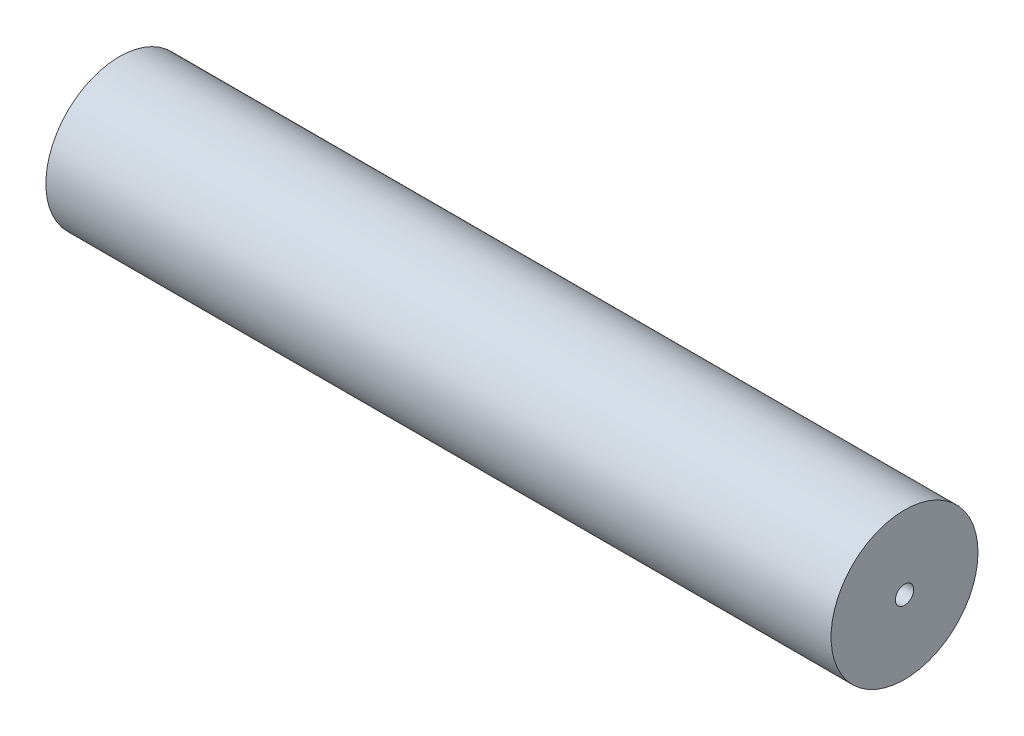
SolidWorks part; units mm, degrees
ref_plane "Front Plane" through (0, 0, 0) normal (0, 0, 1) x (1, 0, 0)
ref_plane "Top Plane" through (0, 0, 0) normal (0, 1, 0) x (1, 0, 0)
ref_plane "Right Plane" through (0, 0, 0) normal (1, 0, 0) x (0, 0, -1)
sketch "Sketch1" plane through (0, 0, 0) normal (1, 0, 0) x (0, 0, -1)
  circle A0 centre (0, 0) radius 50.8
  dimension "D1" = 101.6
extrude "Boss-Extrude1" add sketch "Sketch1" along normal mid plane 542.925
sketch "Sketch2" plane through (-271.4625, 0, 0) normal (-1, 0, 0) x (0, 0, 1)
  circle A0 centre (0, 0) radius 6.35
  dimension "D1" = 12.7
extrude "Cut-Extrude1" cut sketch "Sketch2" against normal through all
